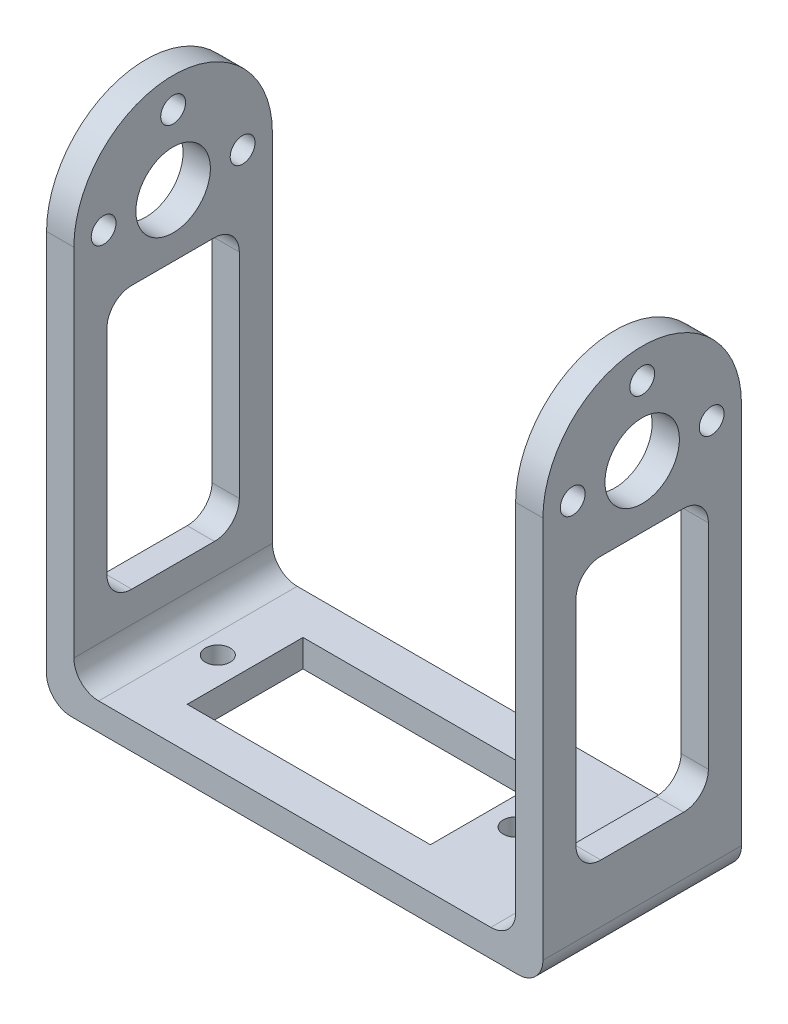
SolidWorks part; units mm, degrees
material "1060 Alloy"
ref_plane "Front Plane" through (0, 0, 0) normal (0, 0, 1) x (1, 0, 0)
ref_plane "Top Plane" through (0, 0, 0) normal (0, 1, 0) x (1, 0, 0)
ref_plane "Right Plane" through (0, 0, 0) normal (1, 0, 0) x (0, 0, -1)
sketch "Sketch1" plane through (0, 0, 0) normal (0, 1, 0) x (1, 0, 0)
  line L1 (-30, -12) -> (30, -12)
  line L2 (-30, -12) -> (-30, 12)
  line L3 (-30, 12) -> (30, 12)
  line L4 (30, -12) -> (30, 12)
  line L5 (-30, -12) -> (30, 12) construction
  line L6 (-30, 12) -> (30, -12) construction
  point P0 (0, 0)
  dimension "D1" = 60
  dimension "D2" = 24
extrude "Boss-Extrude1" add sketch "Sketch1" along normal blind 3.3
sketch "Sketch2" plane through (0, 0, 0) normal (0, 1, 0) x (1, 0, 0)
  line L0 (-30, -12) -> (30, -12) construction
  line L1 (30, 12) -> (26.7, 12)
  line L2 (30, 12) -> (30, -12)
  line L3 (30, -12) -> (26.7, -12)
  line L4 (26.7, 12) -> (26.7, -12)
  dimension "D1" = 3.3
extrude "Boss-Extrude2" add sketch "Sketch2" along normal blind 61.3
sketch "Sketch3" plane through (30, 0, 0) normal (1, 0, 0) x (0, 0, -1)
  line L0 (0, 10) -> (0, 41.8) construction
  line L1 (8, 10) -> (-8, 10)
  line L2 (8, 10) -> (8, 41.8)
  line L3 (8, 41.8) -> (-8, 41.8)
  line L4 (-8, 10) -> (-8, 41.8)
  line L5 (0, 55) -> (0, -55) construction
  line L6 (55, 0) -> (-55, 0) construction
  dimension "D1" = 31.8
  dimension "D2" = 16
  dimension "D3" = 10
extrude "Cut-Extrude1" cut sketch "Sketch3" against normal up to surface (3.3 mm away) up to face at (26.7, 32.3, 0)
sketch "Sketch4" plane through (30, 0, 0) normal (1, 0, 0) x (0, 0, -1)
  line L0 (0, 33) -> (0, -33) construction
  line L1 (12, 61.3) -> (12, 0) construction
  line L2 (-12, 61.3) -> (12, 61.3) construction
  line L3 (12, 49.3) -> (-12, 49.3) construction
  line L4 (12, 49.3) -> (12, 61.3)
  line L5 (12, 61.3) -> (-12, 61.3)
  line L6 (-12, 61.3) -> (-12, 49.3)
  arc A0 (12, 49.3) -> (-12, 49.3) centre (0, 49.3) ccw
  line M6 (12, 0) -> (12, 61.3)
  line M7 (12, 61.3) -> (-12, 61.3)
  line M8 (-12, 61.3) -> (-12, 0)
extrude "Cut-Extrude2" cut sketch "Sketch4" against normal up to surface (3.3 mm away) contours A0 M6 M7 | A0 L5 M8 up to face at (26.7, 25.9, 0)
sketch "Sketch5" plane through (30, 0, 0) normal (1, 0, 0) x (0, 0, -1)
  line L0 (0, 33) -> (0, -33) construction
  circle A0 centre (0, 49.3) radius 4.5
  circle A1 centre (8.4, 49.3) radius 1.5
  circle A2 centre (0, 57.7) radius 1.5
  circle A3 centre (-8.4, 49.3) radius 1.5
  point P8 (0, 44.8)
  point P9 (0, 49.3)
  point P16 (0, 49.3)
  dimension "D1" = 9
  dimension "D2" = 3
  dimension "D4" = 8.4
  dimension "D5" = 3
extrude "Cut-Extrude3" cut sketch "Sketch5" against normal up to surface (3.3 mm away) up to face at (26.7, 25.9, 0)
sketch "Sketch7" plane through (0, 0, 0) normal (0, 1, 0) x (1, 0, 0)
  line L0 (-33, 0) -> (33, 0) construction
  line L1 (11.4, 7) -> (-18, 7)
  line L2 (11.4, 7) -> (11.4, -7)
  line L3 (11.4, -7) -> (-18, -7)
  line L4 (-18, 7) -> (-18, -7)
  line L5 (11.4, 7) -> (-18, -7) construction
  line L6 (11.4, -7) -> (-18, 7) construction
  line L7 (-3.3, 7) -> (-3.3, -7) construction
  line L8 (-18, 0) -> (11.4, 0) construction
  line L9 (-30, 12) -> (-30, -12) construction
  circle A0 centre (-21.3, 0) radius 1.5
  circle A1 centre (14.7, 0) radius 1.5
  dimension "D1" = 36
  dimension "D2" = 3
  dimension "D3" = 29.4
  dimension "D4" = 14
  dimension "D5" = 12
extrude "Cut-Extrude4" cut sketch "Sketch7" along normal up to surface (3.3 mm away) up to face at (-1.65, 3.3, 0)
mirror "Mirror2" about plane through (0, 0, 0) normal (1, 0, 0) of "Cut-Extrude3", "Cut-Extrude2", "Cut-Extrude1", "Boss-Extrude2"
fillet "Fillet1" radius 3 12 edges at (28.35, 10, -8) (-28.35, 41.8, 8) (-28.35, 10, -8) (-28.35, 10, 8) (28.35, 10, 8) (28.35, 41.8, 8) (-28.35, 41.8, -8) (28.35, 41.8, -8) (-26.7, 3.3, 0) (26.7, 3.3, 0) (30, 0, 0) (-30, 0, 0)
